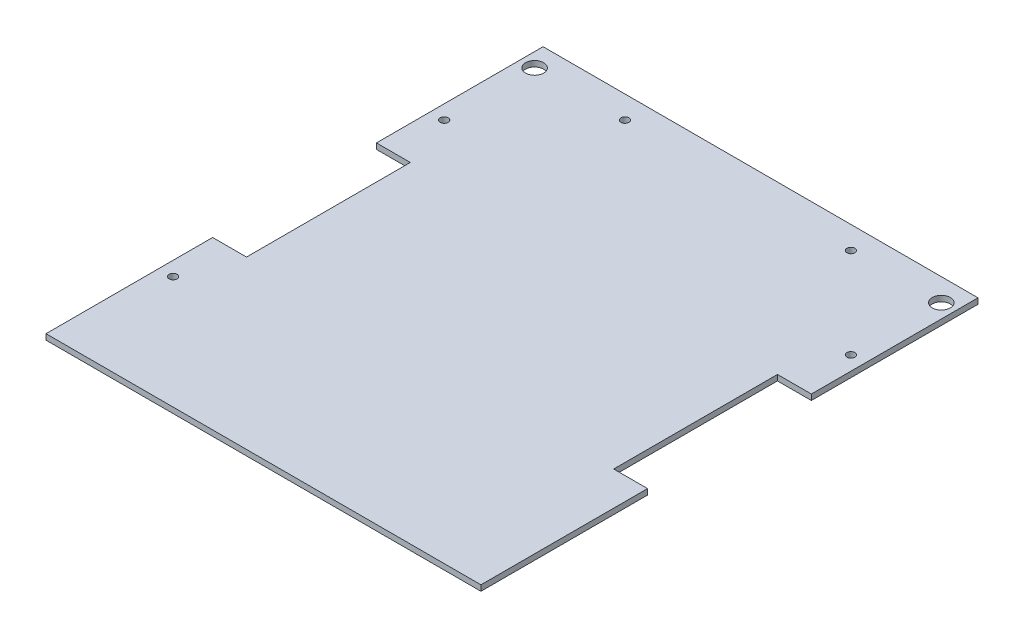
SolidWorks part; units mm, degrees
ref_plane "Front Plane" through (0, 0, 0) normal (0, 0, 1) x (1, 0, 0)
ref_plane "Top Plane" through (0, 0, 0) normal (0, 1, 0) x (1, 0, 0)
ref_plane "Right Plane" through (0, 0, 0) normal (1, 0, 0) x (0, 0, -1)
sketch "Sketch1" plane through (0, 0, 0) normal (0, 1, 0) x (1, 0, 0)
  line L1 (228.6, -139.7) -> (-228.6, -139.7)
  line L2 (228.6, -139.7) -> (228.6, 139.7)
  line L3 (228.6, 139.7) -> (-228.6, 139.7)
  line L4 (-228.6, -139.7) -> (-228.6, 139.7)
  line L5 (228.6, -139.7) -> (-228.6, 139.7) construction
  line L6 (228.6, 139.7) -> (-228.6, -139.7) construction
  point P0 (0, 0)
  dimension "D1" = 279.4
  dimension "D2" = 457.2
extrude "Boss-Extrude1" add sketch "Sketch1" along normal blind 3.175
sketch "Sketch2" plane through (0, 3.175, 0) normal (0, 1, 0) x (1, 0, 0)
  line L0 (-228.6, 139.7) -> (-228.6, -139.7) construction
  line L1 (228.6, 139.7) -> (-228.6, 139.7) construction
  line L3 (-212.3079, 130.5921) -> (-205.9579, 124.2421)
  line L4 (-219.4921, 123.4079) -> (-213.1421, 117.0579)
  line L5 (212.3079, 130.5921) -> (205.9579, 124.2421)
  line L6 (219.4921, 123.4079) -> (213.1421, 117.0579)
  line L17 (0, 76.2) -> (228.6, 76.2) construction
  line L18 (228.6, -139.7) -> (228.6, 139.7) construction
  circle A0 centre (-215.9, 127) radius 2.5 construction
  circle A1 centre (-209.55, 120.65) radius 2.5 construction
  arc A3 (-212.3079, 130.5921) -> (-219.4921, 123.4079) centre (-215.9, 127) ccw
  arc A4 (-213.1421, 117.0579) -> (-205.9579, 124.2421) centre (-209.55, 120.65) ccw
  arc A5 (213.1421, 117.0579) -> (205.9579, 124.2421) centre (209.55, 120.65) cw
  arc A6 (212.3079, 130.5921) -> (219.4921, 123.4079) centre (215.9, 127) cw
  circle A7 centre (-114.3, 127) radius 5.08
  circle A8 centre (114.3, 127) radius 5.08
  circle A9 centre (-215.9, -127) radius 5.08
  circle A10 centre (215.9, -127) radius 5.08
  dimension "D1" = 5
  dimension "D6" = 10.16
  dimension "D2" = 12.7
  dimension "D3" = 12.7
  dimension "D4" = 19.05
  dimension "D5" = 19.05
  dimension "D7" = 101.6
  dimension "D8" = 254
  dimension "D12" = 50.8
extrude "Cut-Extrude1" cut sketch "Sketch2" against normal blind 3.175
sketch "Sketch4" plane through (0, 3.175, 0) normal (0, 1, 0) x (1, 0, 0)
  line L0 (0, 0) -> (0, 139.7) construction
  line L1 (228.6, 139.7) -> (-228.6, 139.7) construction
  line L2 (-228.6, 139.7) -> (-228.6, -139.7) construction
  circle A0 centre (-196.85, 127) radius 2.25
  circle A1 centre (-215.9, 107.95) radius 2.25
  circle A2 centre (196.85, 127) radius 2.25
  circle A3 centre (215.9, 107.95) radius 2.25
  dimension "D3" = 4.5
  dimension "D1" = 12.7
  dimension "D2" = 31.75
  dimension "D4" = 12.7
  dimension "D5" = 31.75
extrude "Cut-Extrude3" cut sketch "Sketch4" against normal blind 25.4
sketch "Sketch6" plane through (0, 3.175, 0) normal (0, 1, 0) x (1, 0, 0)
  line L0 (0, 139.7) -> (0, -139.7) construction
  line L1 (228.6, 139.7) -> (-228.6, 139.7) construction
  line L2 (-228.6, -139.7) -> (228.6, -139.7) construction
  line L3 (-228.6, 139.7) -> (-228.6, -139.7) construction
  line L4 (-114.3, 132.08) -> (-114.3, -139.7) construction
  circle A0 centre (-215.9, 76.2) radius 2.25
  circle A1 centre (-215.9, 0) radius 2.25
  circle A2 centre (-215.9, -88.9) radius 2.25
  circle A7 centre (-114.3, 127) radius 5.08 construction
  circle A8 centre (-114.3, -76.2) radius 2.25
  circle A10 centre (-114.3, 76.2) radius 2.25
  circle A11 centre (-63.5, 127) radius 2.25
  circle A12 centre (63.5, 127) radius 2.25
  circle A13 centre (114.3, 76.2) radius 2.25
  circle A14 centre (215.9, -88.9) radius 2.25
  circle A15 centre (215.9, 0) radius 2.25
  circle A16 centre (215.9, 76.2) radius 2.25
  dimension "D1" = 4.5
  dimension "D2" = 4.5
  dimension "D3" = 4.5
  dimension "D7" = 4.5
  dimension "D8" = 4.5
  dimension "D9" = 4.5
  dimension "D10" = 63.5
  dimension "D11" = 63.5
  dimension "D4" = 12.7
  dimension "D5" = 12.7
  dimension "D6" = 12.7
  dimension "D12" = 12.7
  dimension "D13" = 50.8
  dimension "D14" = 139.7
  dimension "D15" = 63.5
  dimension "D16" = 63.5
extrude "Cut-Extrude5" cut sketch "Sketch6" against normal blind 637.032
sketch "Sketch7" plane through (0, 3.175, 0) normal (0, 1, 0) x (1, 0, 0)
  line L0 (-114.3, -139.7) -> (-114.3, 139.7) construction
  line L1 (-228.6, -139.7) -> (228.6, -139.7) construction
  line L2 (228.6, 139.7) -> (-228.6, 139.7) construction
  line L3 (-104.775, 44.45) -> (-104.775, -44.45)
  line L4 (-123.825, 107.95) -> (-104.775, 107.95) construction
  line L5 (-123.825, 107.95) -> (-123.825, 44.45)
  line L6 (-123.825, 44.45) -> (-104.775, 44.45)
  line L7 (-104.775, 107.95) -> (-104.775, 44.45)
  line L12 (-104.775, -107.95) -> (-123.825, -107.95)
  line L13 (-104.775, -107.95) -> (-104.775, -44.45)
  line L14 (-104.775, -44.45) -> (-123.825, -44.45)
  line L15 (-123.825, -107.95) -> (-123.825, -44.45)
  line L16 (-104.775, -107.95) -> (-123.825, -44.45) construction
  line L17 (-104.775, -44.45) -> (-123.825, -107.95) construction
  line L18 (-123.825, 107.95) -> (-123.825, 139.7)
  line L19 (-123.825, -107.95) -> (-123.825, -139.7)
  line L20 (-122.2375, -107.95) -> (-122.2375, -139.7)
  line L21 (-122.2375, -107.95) -> (-122.2375, -46.0375)
  line L22 (-103.1875, -46.0375) -> (-122.2375, -46.0375)
  line L23 (-103.1875, 46.0375) -> (-103.1875, -46.0375)
  line L24 (-122.2375, 46.0375) -> (-103.1875, 46.0375)
  line L25 (-122.2375, 107.95) -> (-122.2375, 46.0375)
  line L26 (-122.2375, 107.95) -> (-122.2375, 139.7)
  line L27 (0, 0) -> (0, 139.7) construction
  line L28 (122.2375, -107.95) -> (122.2375, -139.7)
  line L29 (122.2375, -107.95) -> (122.2375, -46.0375)
  line L30 (103.1875, -46.0375) -> (122.2375, -46.0375)
  line L31 (103.1875, 46.0375) -> (103.1875, -46.0375)
  line L32 (122.2375, 46.0375) -> (103.1875, 46.0375)
  line L33 (122.2375, 107.95) -> (122.2375, 46.0375)
  line L34 (122.2375, 107.95) -> (122.2375, 139.7)
  circle A0 centre (-114.3, 127) radius 5.08 construction
  circle A1 centre (-114.3, 127) radius 5.08
  circle A2 centre (-114.3, 76.2) radius 2.25 construction
  circle A3 centre (-114.3, 76.2) radius 2.25
  circle A4 centre (-114.3, -76.2) radius 2.25 construction
  circle A5 centre (-114.3, -76.2) radius 2.25
  circle A6 centre (-114.3, 19.05) radius 2.25
  circle A7 centre (-114.3, -19.05) radius 2.25
  circle A8 centre (114.3, -76.2) radius 2.25
  point P17 (-114.3, 44.45)
  point P23 (-123.825, 76.2)
  circle M4 centre (215.9, -88.9) radius 2.25
  circle M10 centre (-215.9, -88.9) radius 2.25
  circle M11 centre (-215.9, 0) radius 2.25
  circle M12 centre (215.9, 0) radius 2.25
  circle M13 centre (215.9, 76.2) radius 2.25
  circle M14 centre (-215.9, 76.2) radius 2.25
  circle M15 centre (215.9, 107.95) radius 2.25
  circle M16 centre (196.85, 127) radius 2.25
  circle M17 centre (-215.9, 107.95) radius 2.25
  circle M18 centre (-196.85, 127) radius 2.25
  circle M19 centre (-215.9, -127) radius 5.08
  arc M22 (-219.4921, 123.4079) -> (-212.3079, 130.5921) centre (-215.9, 127) cw
  line M23 (-212.3079, 130.5921) -> (-205.9579, 124.2421)
  arc M24 (-205.9579, 124.2421) -> (-213.1421, 117.0579) centre (-209.55, 120.65) cw
  line M25 (-213.1421, 117.0579) -> (-219.4921, 123.4079)
  circle M26 centre (215.9, -127) radius 5.08
  arc M29 (212.3079, 130.5921) -> (219.4921, 123.4079) centre (215.9, 127) cw
  line M30 (219.4921, 123.4079) -> (213.1421, 117.0579)
  arc M31 (213.1421, 117.0579) -> (205.9579, 124.2421) centre (209.55, 120.65) cw
  line M32 (205.9579, 124.2421) -> (212.3079, 130.5921)
  line M33 (-228.6, 139.7) -> (-228.6, -139.7)
  line M34 (-228.6, -139.7) -> (228.6, -139.7)
  line M35 (228.6, -139.7) -> (228.6, 139.7)
  line M36 (228.6, 139.7) -> (-228.6, 139.7)
  dimension "D3" = 25.4
  dimension "D1" = 19.05
  dimension "D2" = 63.5
  dimension "D4" = 25.4
  dimension "D5" = 1.5875
extrude "Cut-Extrude6" cut sketch "Sketch7" against normal blind 25.4 contours L19 L15 L14 L3 L6 L5 L18 A7 A6 M36 M33 M34 M10 M14 M18 M25 M22 M23 M24 M19 M17 M11 | L34 L33 L32 L31 L30 L29 L28 M34 M35 M36 M13 M15 M26 M32 M29 M30 M31 M16 M12 M4 | L25 L26 L18 L5 L6 L7 L24 M36 | L24 L7 L3 L13 L22 L23 | L22 L13 L14 L15 L12 L21 | L20 L12 L19 M34 | A6 | A7
